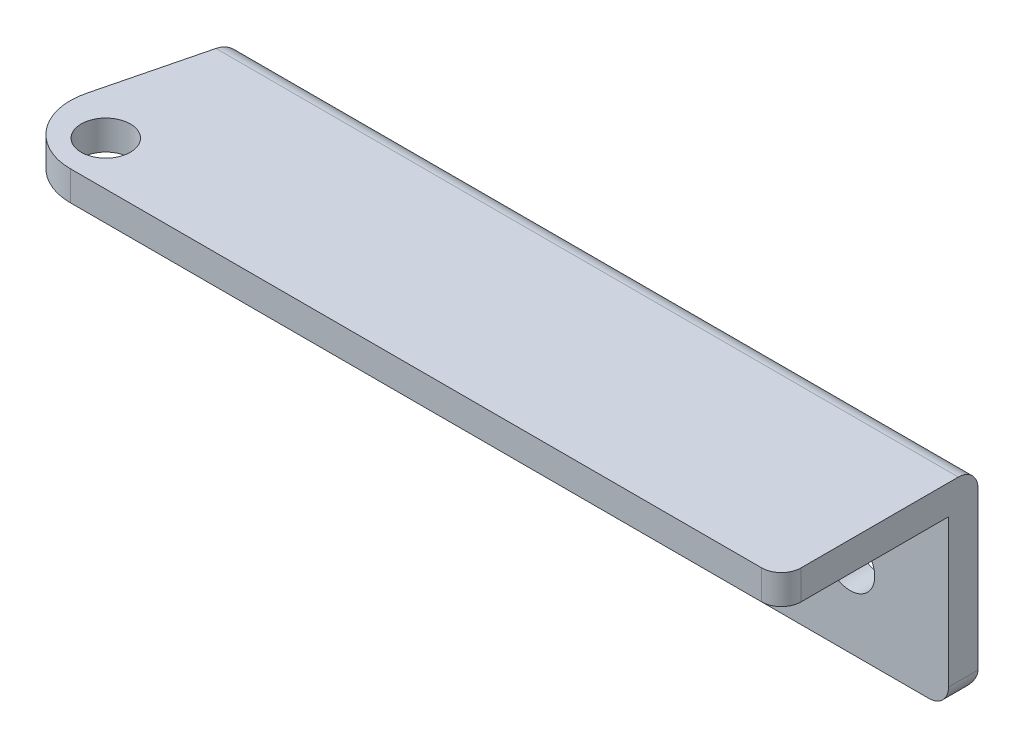
SolidWorks part; units mm, degrees
ref_plane "Front Plane" through (0, 0, 0) normal (0, 0, 1) x (1, 0, 0)
ref_plane "Top Plane" through (0, 0, 0) normal (0, 1, 0) x (1, 0, 0)
ref_plane "Right Plane" through (0, 0, 0) normal (1, 0, 0) x (0, 0, -1)
sketch "Sketch1" plane through (0, 0, 0) normal (0, 1, 0) x (1, 0, 0)
  line L1 (0, 0) -> (75, 0)
  line L2 (0, 0) -> (0, 3)
  line L3 (0, 3) -> (75, 3)
  line L4 (75, 0) -> (75, 3)
  dimension "D1" = 3
  dimension "D2" = 75
extrude "Boss-Extrude1" add sketch "Sketch1" along normal blind 20
sketch "Sketch2" plane through (0, 20, 0) normal (0, 1, 0) x (1, 0, 0)
  line L0 (0, 3) -> (-5, -17)
  line L1 (0, 3) -> (75, 3)
  line L2 (0, 3) -> (0, -17)
  line L3 (0, -17) -> (75, -17)
  line L4 (75, 3) -> (75, -17)
  line L5 (-5, -17) -> (0, -17)
  line M7 (0, 3) -> (0, 0)
  line M8 (0, 0) -> (75, 0)
  dimension "D1" = 20
  dimension "D2" = 5
extrude "Boss-Extrude2" add sketch "Sketch2" against normal blind 3 contours L0 L5 L2 M7 | L4 L2 L3 M8
fillet "Fillet1" radius 6 1 edges at (-5, 18.5, 17)
fillet "Fillet2" radius 2 5 edges at (37.5, 0, -3) (37.5, 20, -3) (0, 0, -1.5) (75, 0, -1.5) (75, 18.5, 17)
sketch "Sketch3" plane through (0, 20, 0) normal (0, 1, 0) x (1, 0, 0)
  line L0 (2.6847, -17) -> (73, -17) construction
  line L1 (-0.5, 1) -> (-3.1362, -9.5448) construction
  circle A0 centre (1.7943, -12.5) radius 2.5
  dimension "D1" = 5
  dimension "D2" = 4.5
  dimension "D3" = 5.5
extrude "Cut-Extrude1" cut sketch "Sketch3" against normal through all
sketch "Sketch4" plane through (0, 0, 0) normal (0, 0, 1) x (1, 0, 0)
  line L0 (75, 17) -> (75, 2) construction
  line L1 (2, 0) -> (73, 0) construction
  circle A0 centre (65, 8) radius 2.5
  circle A1 centre (15, 8) radius 2.5
  point P8 (0, 0)
  dimension "D1" = 5
  dimension "D2" = 10
  dimension "D3" = 50
  dimension "D4" = 8
extrude "Cut-Extrude2" cut sketch "Sketch4" against normal through all
